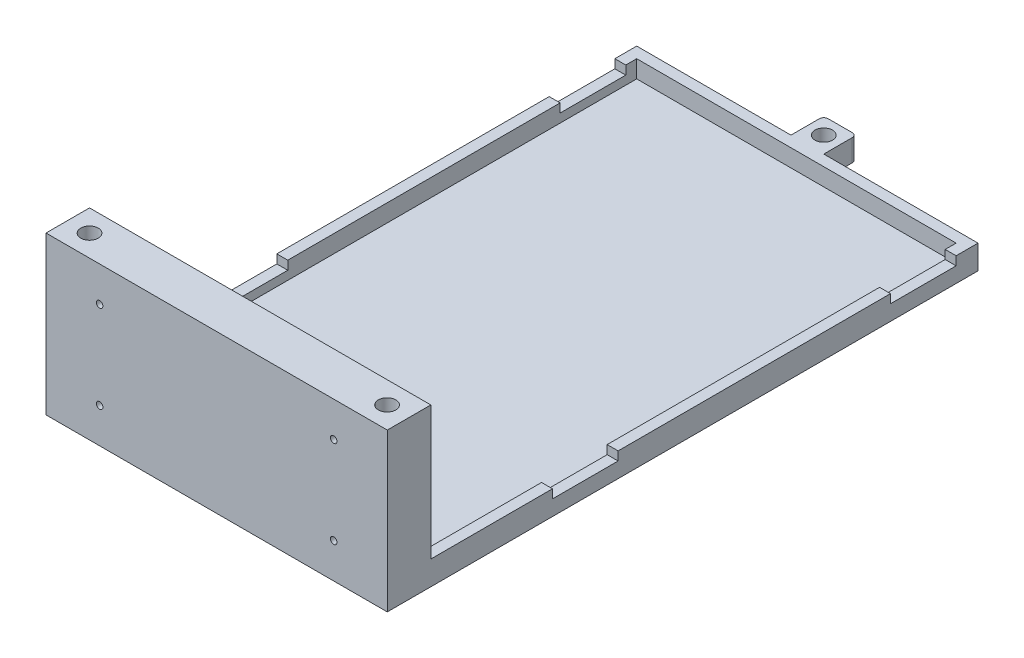
SolidWorks part; units mm, degrees
ref_plane "Front Plane" through (0, 0, 0) normal (0, 0, 1) x (1, 0, 0)
ref_plane "Top Plane" through (0, 0, 0) normal (0, 1, 0) x (1, 0, 0)
ref_plane "Right Plane" through (0, 0, 0) normal (1, 0, 0) x (0, 0, -1)
sketch "Sketch1" plane through (0, 0, 0) normal (0, 1, 0) x (1, 0, 0)
  line L0 (-78, -130) -> (-78, -140)
  line L2 (-78, -130) -> (-78, 130)
  line L3 (-78, 130) -> (78, 130)
  line L4 (78, -130) -> (78, 130)
  line L5 (-78, -130) -> (78, 130) construction
  line L6 (-78, 130) -> (78, -130) construction
  line L7 (-78, -140) -> (78, -140)
  line L8 (78, -140) -> (78, -130)
  point P0 (0, 0)
  dimension "D1" = 260
  dimension "D2" = 156
  dimension "D3" = 10
extrude "Boss-Extrude1" add sketch "Sketch1" along normal blind 3
sketch "Sketch2" plane through (0, 3, 0) normal (0, 1, 0) x (1, 0, 0)
  line L0 (78, -140) -> (78, 130) construction
  line L1 (-73, -120.1041) -> (73, -120.1041) construction
  line L2 (-73, -120.1041) -> (-73, 125)
  line L3 (-73, 125) -> (73, 125)
  line L4 (73, -120.1041) -> (73, 125)
  line L5 (-73, -120.1041) -> (-78, -120.1041)
  line L6 (73, -120.1041) -> (78, -120.1041)
  line L8 (-78, 130) -> (-78, -140) construction
  line L9 (78, 130) -> (-78, 130) construction
  line L10 (78, -120.1041) -> (78, 130)
  line L12 (-78, 130) -> (-78, -120.1041)
  line L13 (78, 130) -> (-78, 130)
  line L14 (78, -130.1041) -> (-78, -130.1041) construction
  line L16 (78, -140) -> (78, 130) construction
  line L17 (-78, 130) -> (-78, -140) construction
  point P0 (0, 0)
  dimension "D1" = 5
  dimension "D2" = 5
  dimension "D3" = 10
  dimension "D4" = 5
extrude "Boss-Extrude2" add sketch "Sketch2" along normal blind 8
sketch "Sketch3" plane through (0, 3, 0) normal (0, 1, 0) x (1, 0, 0)
  line L0 (73, -120.1041) -> (78, -120.1041) construction
  line L5 (78, -140) -> (78, -120.1041) construction
  line L6 (-78, -140) -> (78, -140) construction
  line L7 (-78, -120.1041) -> (-78, -140) construction
  line L8 (-78, -120.1041) -> (-73, -120.1041) construction
  line L9 (73, -120.1041) -> (78, -120.1041)
  line L10 (78, -140) -> (78, -120.1041)
  line L11 (-78, -140) -> (78, -140)
  line L12 (-78, -120.1041) -> (-78, -140)
  line L13 (-78, -120.1041) -> (-73, -120.1041)
  line L14 (-73, -120.1041) -> (73, -120.1041)
extrude "Boss-Extrude3" add sketch "Sketch3" along normal blind 69
sketch "Sketch4" plane through (0, 72, 0) normal (0, 1, 0) x (1, 0, 0)
  line L1 (0, -120.1041) -> (0, -140) construction
  line L4 (73, -120.1041) -> (-73, -120.1041) construction
  line L5 (-78, -120.1041) -> (-78, -140) construction
  line L6 (78, -120.1041) -> (-78, -120.1041) construction
  line L7 (-78, -140) -> (78, -140) construction
  circle A0 centre (-68, -130.1041) radius 4
  circle A2 centre (68, -130.1041) radius 4
  dimension "D1" = 8
  dimension "D2" = 10
  dimension "D3" = 10
extrude "Cut-Extrude1" cut sketch "Sketch4" against normal blind 10
sketch "Sketch5" plane through (0, 11, 0) normal (0, 1, 0) x (1, 0, 0)
  line L0 (-78, 105) -> (-73, 105) construction
  line L1 (-78, 130) -> (-78, -120.1041) construction
  line L2 (-73, -120.1041) -> (-73, 125) construction
  line L3 (-78, -49.5) -> (-73, -49.5) construction
  line L4 (-73, -120.1041) -> (-73, 125) construction
  line L5 (-73, 125) -> (73, 125) construction
  line L6 (0, 125) -> (0, -120.1041) construction
  line L7 (78, -120.1041) -> (-78, -120.1041) construction
  line L8 (-78, 90) -> (-73, 90)
  line L9 (-78, 90) -> (-78, 120)
  line L10 (-78, 120) -> (-73, 120)
  line L11 (-73, 90) -> (-73, 120)
  line L12 (-78, 90) -> (-73, 120) construction
  line L13 (-78, 120) -> (-73, 90) construction
  line L14 (-78, -64.5) -> (-73, -64.5)
  line L15 (-78, -64.5) -> (-78, -34.5)
  line L16 (-78, -34.5) -> (-73, -34.5)
  line L17 (-73, -64.5) -> (-73, -34.5)
  line L18 (-78, -64.5) -> (-73, -34.5) construction
  line L19 (-78, -34.5) -> (-73, -64.5) construction
  line L34 (78, -34.5) -> (73, -34.5)
  line L38 (73, -64.5) -> (73, -34.5)
  line L39 (78, -64.5) -> (73, -64.5)
  line L40 (78, -64.5) -> (78, -34.5)
  line L41 (78, 120) -> (73, 120)
  line L42 (73, 90) -> (73, 120)
  line L43 (78, 90) -> (73, 90)
  line L44 (78, 90) -> (78, 120)
  point P14 (-75.5, 105)
  point P19 (-75.5, -49.5)
  dimension "D1" = 20
  dimension "D2" = 154.5
  dimension "D3" = 30
  dimension "D4" = 30
extrude "Cut-Extrude2" cut sketch "Sketch5" against normal blind 4
sketch "Sketch6" plane through (0, 11, 0) normal (0, 1, 0) x (1, 0, 0)
  line L0 (78, 130) -> (-78, 130) construction
  line L1 (-7.5, 145) -> (7.5, 145)
  line L2 (-7.5, 145) -> (-7.5, 130)
  line L3 (-7.5, 130) -> (7.5, 130)
  line L4 (7.5, 145) -> (7.5, 130)
  line L5 (-7.5, 145) -> (7.5, 130) construction
  line L6 (-7.5, 130) -> (7.5, 145) construction
  line L7 (-78, 130) -> (-78, 120) construction
  point P0 (0, 137.5)
  dimension "D1" = 15
  dimension "D2" = 15
  dimension "D3" = 78
extrude "Boss-Extrude4" add sketch "Sketch6" against normal blind 10
sketch "Sketch7" plane through (0, 11, 0) normal (0, 1, 0) x (1, 0, 0)
  line L0 (7.5, 145) -> (-7.5, 145) construction
  line L1 (-7.5, 145) -> (-7.5, 130) construction
  circle A0 centre (0, 137.5) radius 4
  dimension "D1" = 8
  dimension "D2" = 7.5
  dimension "D3" = 7.5
extrude "Cut-Extrude3" cut sketch "Sketch7" against normal blind 10
fillet "Fillet1" radius 2 2 edges at (-7.5, 6, -145) (7.5, 6, -145)
sketch "Sketch8" plane through (0, 0, 140) normal (0, 0, 1) x (1, 0, 0)
  line L0 (-78, 72) -> (78, 72) construction
  line L1 (-78, 0) -> (78, 0) construction
  line L2 (78, 72) -> (78, 0) construction
  line L3 (0, 72) -> (0, 0) construction
  circle A0 centre (53.5, 56) radius 1.5
  circle A1 centre (53.5, 16) radius 1.5
  circle A2 centre (-53.5, 16) radius 1.5
  circle A3 centre (-53.5, 56) radius 1.5
  dimension "D2" = 3
  dimension "D6" = 3
  dimension "D1" = 16
  dimension "D3" = 40
  dimension "D4" = 16
  dimension "D5" = 24.5
extrude "Cut-Extrude4" cut sketch "Sketch8" against normal through all
equation "\"t_wall\"= 5mm"
